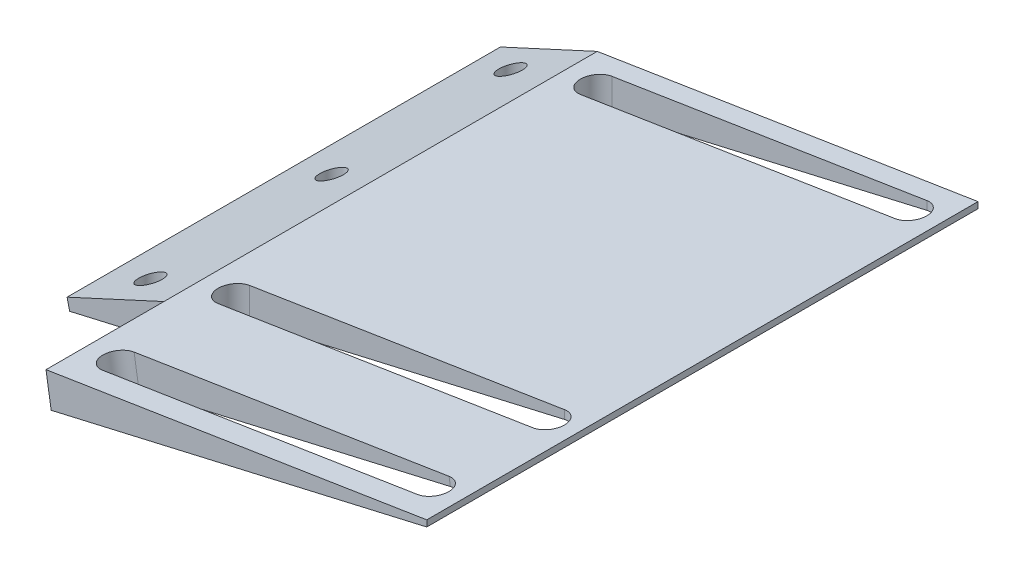
SolidWorks part; units mm, degrees
ref_plane "Front Plane" through (0, 0, 0) normal (0, 0, 1) x (1, 0, 0)
ref_plane "Top Plane" through (0, 0, 0) normal (0, 1, 0) x (1, 0, 0)
ref_plane "Right Plane" through (0, 0, 0) normal (1, 0, 0) x (0, 0, -1)
sketch "Sketch1" plane through (0, 0, 0) normal (0, 0, 1) x (1, 0, 0)
  line L0 (-1000, 0) -> (49000, 0) construction
  line L1 (0, 0) -> (-142.4753, -32.893)
  line L2 (0, 0) -> (-118.5226, -18.7721)
  line L3 (-118.5226, -18.7721) -> (-143.1192, -30.1042)
  line L4 (-143.1192, -30.1042) -> (-142.4753, -32.893)
  dimension "D1" = 13
  dimension "D2" = 9
  dimension "D4" = 120
extrude "Boss-Extrude1" add sketch "Sketch1" along normal blind 110
sketch "Sketch2" plane through (0, 0, 110) normal (0, 0, 1) x (1, 0, 0)
  line L0 (-21.8204, -5.0376) -> (-21.8204, -3.456)
  line L1 (-142.4753, -32.893) -> (0, 0) construction
  line L2 (0, 0) -> (-118.5226, -18.7721) construction
  line M2 (0, 0) -> (-118.5226, -18.7721)
  line M5 (-142.4753, -32.893) -> (0, 0)
extrude "Cut-Extrude1" cut sketch "Sketch2" against normal through all and the other way through all contours L0 M5 M2
ref_plane "Plane1" through (0, 10, 0) normal (0, 1, 0) x (1, 0, 0)
sketch "Sketch4" plane through (0, 10, 0) normal (0, 1, 0) x (1, 0, 0)
  line L0 (-29.8204, -101) -> (-109.8204, -101) construction
  line L1 (-29.8204, -105) -> (-109.8204, -105)
  line L2 (-29.8204, -97) -> (-109.8204, -97)
  line L3 (-1021.8204, -55) -> (48978.1796, -55) construction
  line L4 (-21.8204, 0) -> (-21.8204, -110) construction
  line L5 (-29.8204, -9) -> (-109.8204, -9) construction
  line L6 (-29.8204, -5) -> (-109.8204, -5)
  line L7 (-29.8204, -13) -> (-109.8204, -13)
  arc A0 (-29.8204, -105) -> (-29.8204, -97) centre (-29.8204, -101) ccw
  arc A1 (-109.8204, -97) -> (-109.8204, -105) centre (-109.8204, -101) ccw
  arc A2 (-29.8204, -5) -> (-29.8204, -13) centre (-29.8204, -9) cw
  arc A3 (-109.8204, -13) -> (-109.8204, -5) centre (-109.8204, -9) cw
  circle A4 centre (-130.9956, -101) radius 3
  circle A5 centre (-131.5382, -9) radius 3
  circle A6 centre (-130.9956, -55) radius 3
  point P2 (-69.8204, -101)
  point P12 (-21.8204, -55)
  point P14 (-69.8204, -9)
  dimension "D1" = 8
  dimension "D2" = 80
  dimension "D3" = 50
  dimension "D4" = 8
extrude "Cut-Extrude2" cut sketch "Sketch4" against normal through all both and the other way through all
sketch "Sketch5" plane through (0, 0, 110) normal (0, 0, 1) x (1, 0, 0)
  line L5 (-142.4753, -32.893) -> (-21.8204, -5.0376)
  line L6 (-21.8204, -5.0376) -> (-21.8204, -3.456)
  line L7 (-21.8204, -3.456) -> (-118.5226, -18.7721)
  line L8 (-118.5226, -18.7721) -> (-143.1192, -30.1042)
  line L9 (-143.1192, -30.1042) -> (-142.4753, -32.893)
  line L10 (-142.4753, -32.893) -> (-21.8204, -5.0376)
  line L11 (-21.8204, -5.0376) -> (-21.8204, -3.456)
  line L12 (-21.8204, -3.456) -> (-118.5226, -18.7721)
  line L13 (-118.5226, -18.7721) -> (-143.1192, -30.1042)
  line L14 (-143.1192, -30.1042) -> (-142.4753, -32.893)
  dimension "D1" = 0
extrude "Boss-Extrude2" add sketch "Sketch5" along normal blind 30
sketch "Sketch6" plane through (0, 0, 0) normal (-0.1564, 0.9877, 0) x (0.9877, 0.1564, 0)
  line L0 (-30.1921, -130.3241) -> (-111.1893, -130.3241) construction
  line L1 (-30.1921, -134.3241) -> (-111.1893, -134.3241)
  line L2 (-30.1921, -126.3241) -> (-111.1893, -126.3241)
  line L4 (-120, -140) -> (-146.1277, -140)
  line L5 (-120, -140) -> (-120, -110.0454)
  line L6 (-120, -110.0454) -> (-146.1277, -110.0454)
  line L7 (-146.1277, -140) -> (-146.1277, -110.0454)
  arc A0 (-30.1921, -134.3241) -> (-30.1921, -126.3241) centre (-30.1921, -130.3241) ccw
  arc A1 (-111.1893, -126.3241) -> (-111.1893, -134.3241) centre (-111.1893, -130.3241) ccw
  point P2 (-70.6907, -130.3241)
  dimension "D1" = 8
extrude "Cut-Extrude3" cut sketch "Sketch6" against normal through all both and the other way through all
